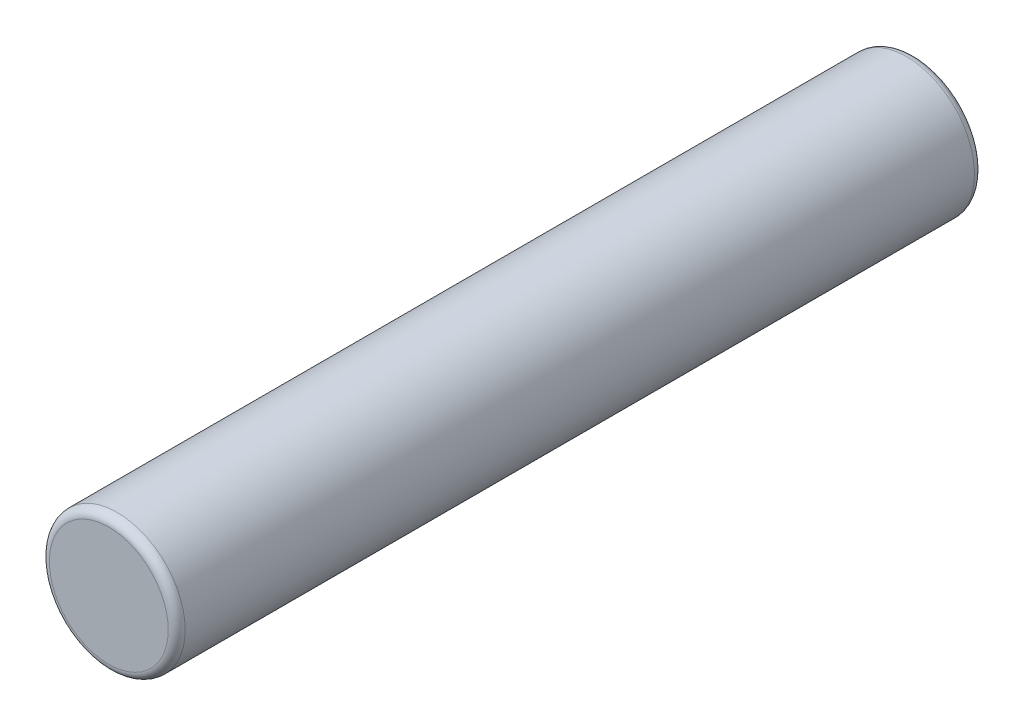
SolidWorks part; units mm, degrees
ref_plane "Front Plane" through (0, 0, 0) normal (0, 0, 1) x (1, 0, 0)
ref_plane "Top Plane" through (0, 0, 0) normal (0, 1, 0) x (1, 0, 0)
ref_plane "Right Plane" through (0, 0, 0) normal (1, 0, 0) x (0, 0, -1)
sketch "Sketch2" plane through (0, 0, 0) normal (0, 0, 1) x (1, 0, 0)
  circle A0 centre (0, 0) radius 0.8
  dimension "D1" = 1.6
extrude "Boss-Extrude1" add sketch "Sketch2" along normal blind 9.5
fillet "Fillet1" radius 0.1 2 edges at (0.8, 0, 0) (0.8, 0, 9.5)
